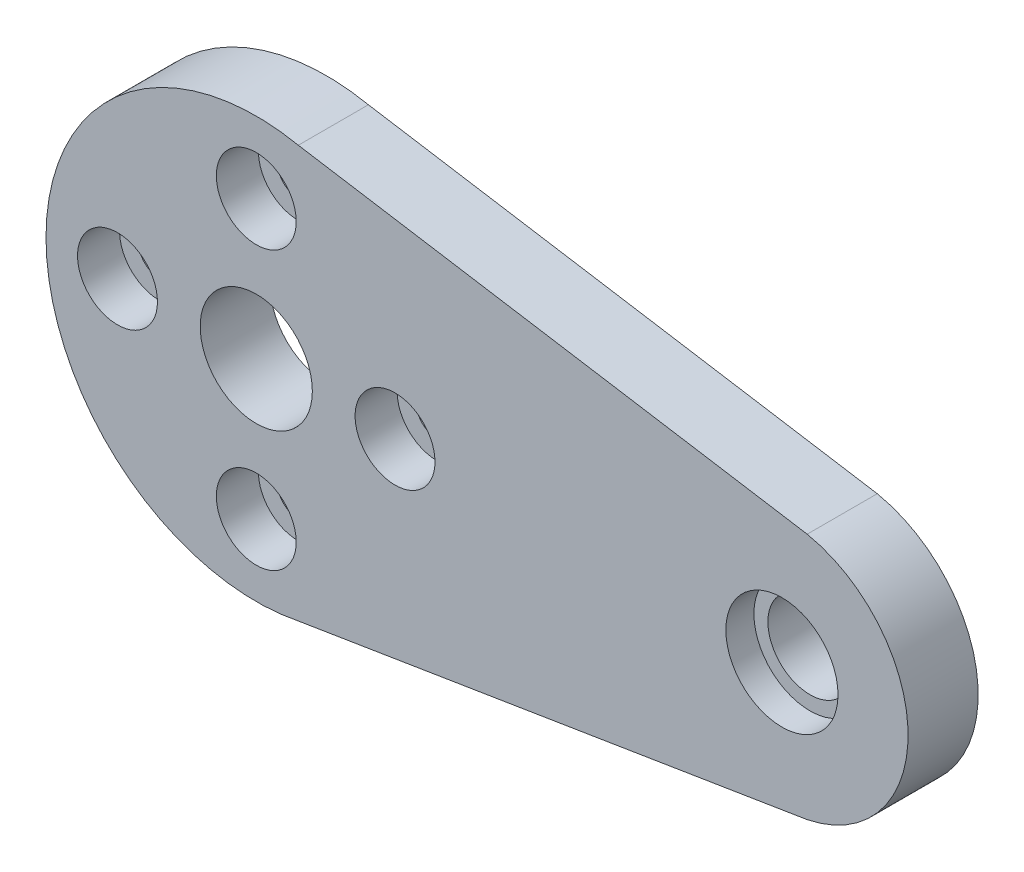
SolidWorks part; units mm, degrees
ref_plane "前视基准面" through (0, 0, 0) normal (0, 0, 1) x (1, 0, 0)
ref_plane "上视基准面" through (0, 0, 0) normal (0, 1, 0) x (1, 0, 0)
ref_plane "右视基准面" through (0, 0, 0) normal (1, 0, 0) x (0, 0, -1)
sketch "草图1" plane through (0, 0, 0) normal (0, 0, 1) x (1, 0, 0)
  line L0 (23.05, 8.6518) -> (-13.25, 14.5306)
  line L1 (-13.25, -14.8633) -> (23.05, -8.9845)
  line L2 (-41.5446, -0.1664) -> (35.8188, -0.1664) construction
  line L3 (0, 18.1488) -> (0, -24.3763) construction
  arc A0 (23.05, -8.9845) -> (23.05, 8.6518) centre (21.25, -0.1664) ccw
  arc A1 (-13.25, 14.5306) -> (-13.25, -14.8633) centre (-16.25, -0.1664) ccw
  circle A4 centre (21.25, -0.1664) radius 4
  circle A5 centre (-16.25, -0.1664) radius 4
  dimension "D2" = 37.5
  dimension "D3" = 21.25
  dimension "D4" = 8
  dimension "D5" = 8
  dimension "D6" = 9
  dimension "D7" = 15
  dimension "D1" = 0.1664
extrude "凸台-拉伸1" add sketch "草图1" along normal blind 5
sketch "草图2" plane through (0, 0, 0) normal (0, 0, -1) x (-1, 0, 0)
  circle A5 centre (-21.25, -0.1664) radius 3
  circle A6 centre (-21.25, -0.1664) radius 4
  dimension "D3" = 6
extrude "凸台-拉伸2" add sketch "草图2" against normal blind 3
sketch "草图3" plane through (0, 0, 5) normal (0, 0, 1) x (1, 0, 0)
  line L0 (-42.4745, -0.1664) -> (8.4844, -0.1664) construction
  line L1 (-16.25, 25.3192) -> (-16.25, -22.355) construction
  circle A0 centre (-16.25, -0.1664) radius 9.9 construction
  circle A1 centre (-16.25, 9.7336) radius 1.5
  circle A2 centre (-6.35, -0.1664) radius 1.5
  circle A3 centre (-26.15, -0.1664) radius 1.5
  circle A4 centre (-16.25, -10.0664) radius 1.5
  dimension "D1" = 19.8
  dimension "D2" = 3
  dimension "D3" = 3
  dimension "D4" = 3
  dimension "D5" = 3
extrude "切除-拉伸1" cut sketch "草图3" against normal blind 10
sketch "草图4" plane through (0, 0, 5) normal (0, 0, 1) x (1, 0, 0)
  circle A0 centre (-16.25, 9.7336) radius 2.85
  circle A1 centre (-26.15, -0.1664) radius 2.85
  circle A2 centre (-6.35, -0.1664) radius 2.85
  circle A3 centre (-16.25, -10.0664) radius 2.85
  dimension "D1" = 5.7
  dimension "D2" = 5.7
  dimension "D3" = 5.7
  dimension "D4" = 5.7
extrude "切除-拉伸2" cut sketch "草图4" against normal blind 3
